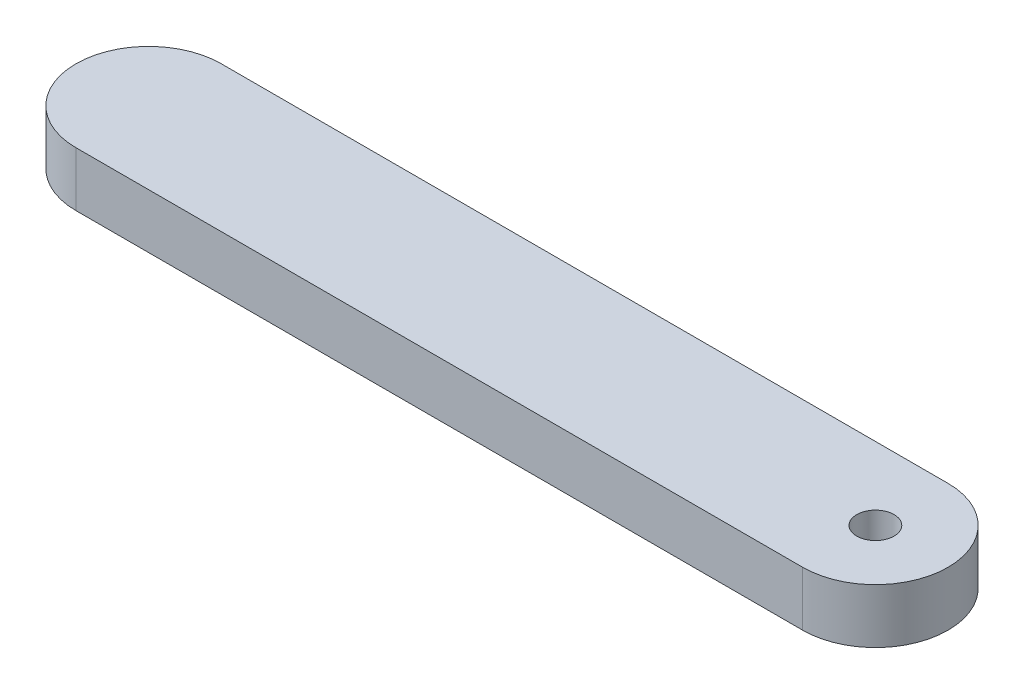
SolidWorks part; units mm, degrees
material "6061-T6 (SS)"
ref_plane "Front Plane" through (0, 0, 0) normal (0, 0, 1) x (1, 0, 0)
ref_plane "Top Plane" through (0, 0, 0) normal (0, 1, 0) x (1, 0, 0)
ref_plane "Right Plane" through (0, 0, 0) normal (1, 0, 0) x (0, 0, -1)
sketch "Sketch1" plane through (0, 0, 0) normal (0, 1, 0) x (1, 0, 0)
  line L0 (-63.5, 0) -> (0, 0) construction
  line L1 (-63.5, 6.35) -> (0, 6.35)
  line L2 (-63.5, -6.35) -> (0, -6.35)
  arc A0 (-63.5, 6.35) -> (-63.5, -6.35) centre (-63.5, 0) ccw
  arc A1 (0, -6.35) -> (0, 6.35) centre (0, 0) ccw
  point P2 (-31.75, 0)
  point P9 (-69.85, 0)
  point P10 (6.35, 0)
  dimension "D2" = 76.2
  dimension "D1" = 12.7
extrude "Boss-Extrude2" add sketch "Sketch1" along normal blind 4.7625
hole_wizard "#4 Clearance Hole1" positions "Sketch2" profile "Sketch4" hole size "#4" standard "ANSI Inch" end condition through all
sketch "Sketch2" plane through (0, 4.7625, 0) normal (0, 1, 0) x (1, 0, 0)
  point P0 (0, 0)
sketch "Sketch4" plane through (0, 4.7625, 0) normal (1, 0, 0) x (0, 0, 1)
  line L0 (0, 0) -> (0, 4.7625)
  line L1 (0, 4.7625) -> (1.6319, 4.7625)
  line L2 (1.6319, 4.7625) -> (1.6319, 0)
  line L5 (1.6319, 0) -> (0, 0)
  line L11 (0, -6.35) -> (0, 107.95) construction
  dimension "Thru Hole Dia." = 3.2639
  dimension "Thru Hole Depth" = 4.7625
